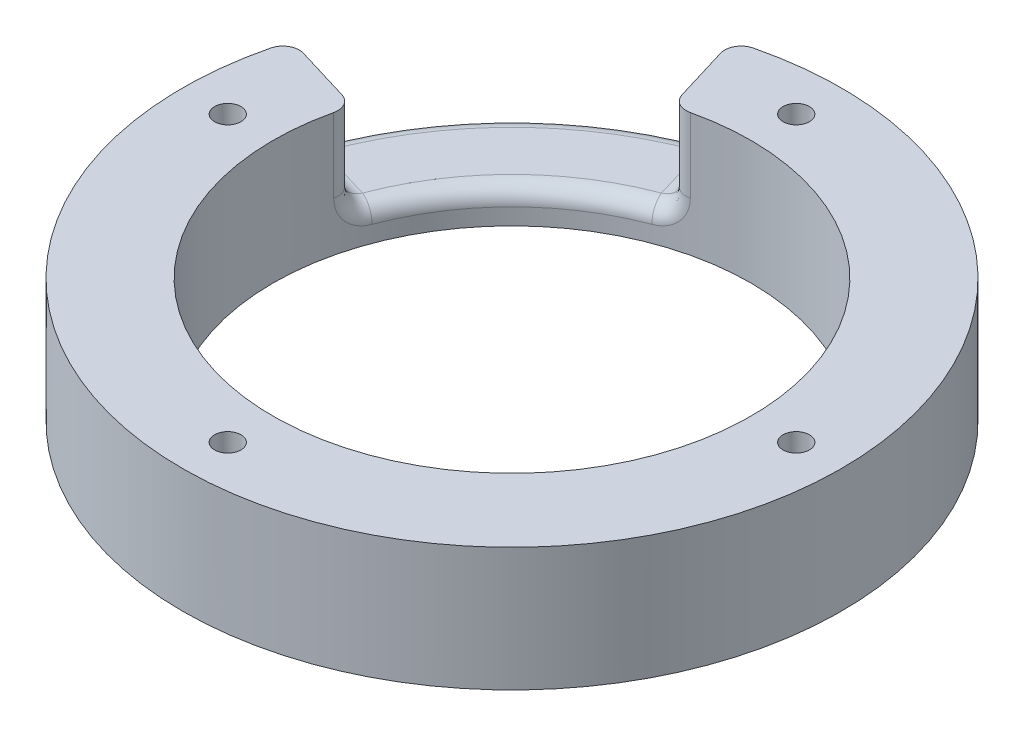
SolidWorks part; units mm, degrees
material "PA 类型 6"
ref_plane "前视基准面" through (0, 0, 0) normal (0, 0, 1) x (1, 0, 0)
ref_plane "上视基准面" through (0, 0, 0) normal (0, 1, 0) x (1, 0, 0)
ref_plane "右视基准面" through (0, 0, 0) normal (1, 0, 0) x (0, 0, -1)
other "Configuration Table"
sketch "草图1" plane through (0, 0, 0) normal (0, 1, 0) x (1, 0, 0)
  circle A0 centre (0, 0) radius 40
  circle A1 centre (0, 0) radius 29
  circle A2 centre (0, 0) radius 34.5 construction
  circle A3 centre (0, 34.5) radius 1.6
  circle A4 centre (34.5, 0) radius 1.6
  circle A5 centre (-34.5, 0) radius 1.6
  circle A6 centre (0, -34.5) radius 1.6
extrude "凸台-拉伸1" add sketch "草图1" along normal blind 15
sketch "草图2" plane through (0, 15, 0) normal (0, 1, 0) x (1, 0, 0)
  line L0 (0, 0) -> (-49.1213, 14.8767) construction
  line L1 (0, 0) -> (-50.5757, -15.3172) construction
  line L2 (0, 0) -> (-13.8036, -45.5781) construction
  line L3 (0, 0) -> (12.4828, -41.2167) construction
  line L4 (-11.5942, 38.2828) -> (-8.4058, 27.755)
  line L5 (-38.2828, 11.5942) -> (-27.755, 8.4058)
  line L6 (0, -55) -> (0, 55) construction
  line L7 (11.5942, 38.2828) -> (8.4058, 27.755)
  line L8 (38.2828, 11.5942) -> (27.755, 8.4058)
  line L9 (-55, 0) -> (55, 0) construction
  line L10 (-38.2828, -11.5942) -> (-27.755, -8.4058)
  line L11 (-11.5942, -38.2828) -> (-8.4058, -27.755)
  line L12 (11.5942, -38.2828) -> (8.4058, -27.755)
  line L13 (38.2828, -11.5942) -> (27.755, -8.4058)
  circle A0 centre (0, -34.5) radius 10 construction
  circle A1 centre (34.5, 0) radius 10 construction
  circle A2 centre (0, 34.5) radius 10 construction
  circle A3 centre (-34.5, 0) radius 10 construction
  arc A4 (-38.2828, 11.5942) -> (-11.5942, 38.2828) centre (0, 0) cw
  circle A5 centre (0, 0) radius 40 construction
  arc A6 (-27.755, 8.4058) -> (-8.4058, 27.755) centre (0, 0) cw
  circle A7 centre (0, 0) radius 29 construction
  arc A8 (27.755, 8.4058) -> (8.4058, 27.755) centre (0, 0) ccw
  arc A9 (38.2828, 11.5942) -> (11.5942, 38.2828) centre (0, 0) ccw
  arc A10 (-27.755, -8.4058) -> (-8.4058, -27.755) centre (0, 0) ccw
  arc A11 (-38.2828, -11.5942) -> (-11.5942, -38.2828) centre (0, 0) ccw
  arc A12 (38.2828, -11.5942) -> (11.5942, -38.2828) centre (0, 0) cw
  arc A13 (27.755, -8.4058) -> (8.4058, -27.755) centre (0, 0) cw
  circle M7 centre (0, 0) radius 40
  circle M8 centre (0, 0) radius 29
extrude "切除-拉伸1" cut sketch "草图2" against normal blind 11 contours L5 L4 M7 M8
fillet "圆角1" radius 2 8 edges at (-28.2843, 4, -28.2843) (-20.5061, 4, -20.5061) (-27.755, 9.5, -8.4058) (-8.4058, 9.5, -27.755) (-38.2828, 9.5, -11.5942) (-11.5942, 9.5, -38.2828) (-33.0189, 4, -10) (-10, 4, -33.0189)
